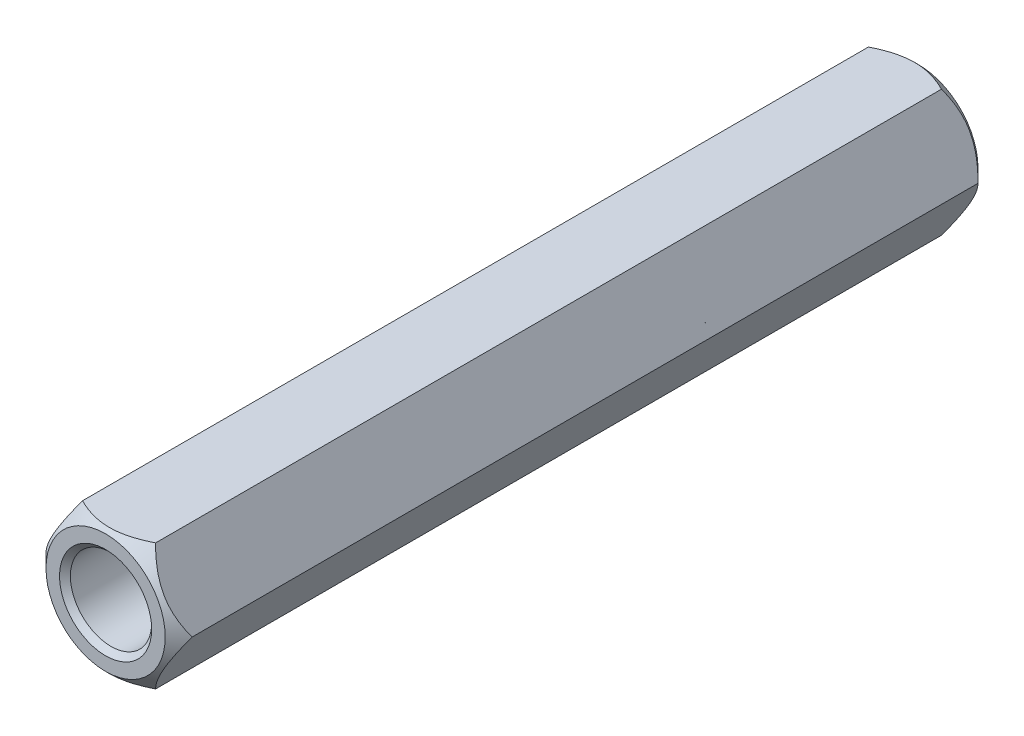
SolidWorks part; units mm, degrees
material "黄铜"
ref_plane "前视基准面" through (0, 0, 0) normal (0, 0, 1) x (1, 0, 0)
ref_plane "上视基准面" through (0, 0, 0) normal (0, 1, 0) x (1, 0, 0)
ref_plane "右视基准面" through (0, 0, 0) normal (1, 0, 0) x (0, 0, -1)
sketch "草图1" plane through (0, 0, 0) normal (0, 0, 1) x (1, 0, 0)
  line L1 (2.6962, 0) -> (1.3481, 2.335)
  line L2 (1.3481, 2.335) -> (-1.3481, 2.335)
  line L3 (-1.3481, 2.335) -> (-2.6962, 0)
  line L4 (-2.6962, 0) -> (-1.3481, -2.335)
  line L5 (-1.3481, -2.335) -> (1.3481, -2.335)
  line L6 (1.3481, -2.335) -> (2.6962, 0)
  circle A0 centre (0, 0) radius 2.335 construction
  circle A1 centre (0, 0) radius 1.5
  dimension "D2" = 3
  dimension "D1" = 4.67
extrude "凸台-拉伸1" add sketch "草图1" along normal blind 30
sketch "草图2" plane through (0, 0, 0) normal (1, 0, 0) x (0, 0, -1)
  line L0 (-0.2772, 1.4228) -> (0.1017, 1.8017)
  line L1 (0.1017, 1.8017) -> (0.1017, 1.4228)
  line L2 (0.1017, 1.4228) -> (-0.2772, 1.4228)
  line L3 (0.0715, 2.1285) -> (-0.9285, 3.1285)
  line L4 (-0.9285, 3.1285) -> (0.0715, 3.1285)
  line L5 (0.0715, 3.1285) -> (0.0715, 2.1285)
  line L6 (0, 1.4228) -> (0, 1.7) construction
  line L7 (0, 0) -> (0, 2.335) construction
  line L8 (0, 2.2) -> (0, 3.1285) construction
  line L9 (-15, 13.9019) -> (-15, -15.4245) construction
  line L11 (0, -2.335) -> (0, 0) construction
  line L12 (-29.7228, 1.4228) -> (-30.1017, 1.8017)
  line L13 (-30.1017, 1.4228) -> (-29.7228, 1.4228)
  line L14 (-30.1017, 1.8017) -> (-30.1017, 1.4228)
  line L15 (-29.0715, 3.1285) -> (-30.0715, 3.1285)
  line L16 (-30.0715, 3.1285) -> (-30.0715, 2.1285)
  line L17 (-30.0715, 2.1285) -> (-29.0715, 3.1285)
  dimension "D1" = 1.7
  dimension "D2" = 2.2
  dimension "D3" = 1
  dimension "D4" = 15
sweep "切除-扫描1" cut profiles "草图2" path edge at (1.5, 0, 0)
